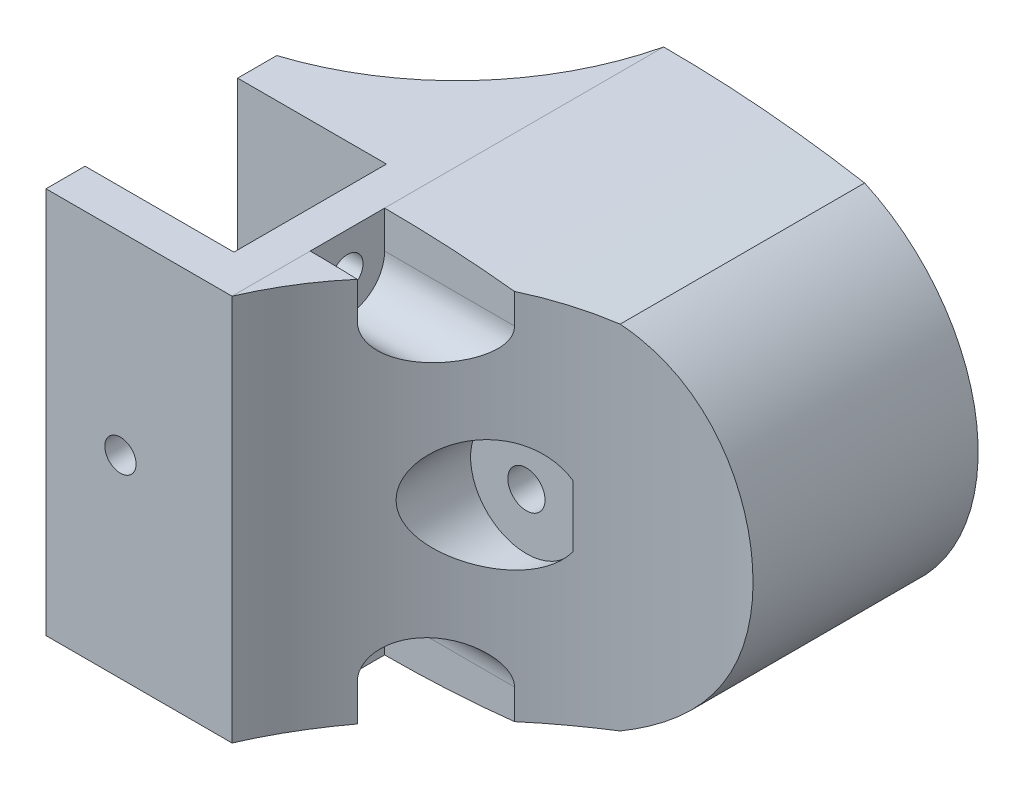
SolidWorks part; units mm, degrees
material "PBT Общее назначение"
ref_plane "Спереди" through (0, 0, 0) normal (0, 0, 1) x (1, 0, 0)
ref_plane "Сверху" through (0, 0, 0) normal (0, 1, 0) x (1, 0, 0)
ref_plane "Справа" through (0, 0, 0) normal (1, 0, 0) x (0, 0, -1)
sketch "Эскиз1" plane through (0, 0, 0) normal (0, 0, 1) x (1, 0, 0)
  line L0 (0, 0) -> (61.556, 0) construction
  line L1 (0, 26) -> (0, -26)
  line L2 (0, 26) -> (52, 26)
  line L3 (0, -26) -> (52, -26)
  line L4 (52, 26) -> (52, -26)
  line L5 (0, 0) -> (52, 0) construction
  dimension "D1" = 52
  dimension "D2" = 52
extrude "Бобышка-Вытянуть1" add sketch "Эскиз1" along normal blind 31
sketch "Эскиз2" plane through (0, 0, 0) normal (-1, 0, 0) x (0, 0, 1)
  line L0 (15.5, 26) -> (15.5, -26) construction
  line L1 (31, 26) -> (0, 26) construction
  line L2 (31, -26) -> (0, -26) construction
  line L3 (5.25, 26) -> (25.75, 26)
  line L4 (5.25, 26) -> (5.25, -26)
  line L5 (25.75, 26) -> (25.75, -26)
  line L6 (5.25, -26) -> (25.75, -26)
  line L7 (15.5, 26) -> (15.5, -26) construction
  dimension "D1" = 20.5
extrude "Вырез-Вытянуть1" cut sketch "Эскиз2" against normal blind 20
sketch "Эскиз3" plane through (52, 0, 0) normal (1, 0, 0) x (0, 0, -1)
  line L0 (-15.5, 26) -> (-15.5, -26) construction
  line L1 (-31, 26) -> (0, 26) construction
  line L2 (-31, -26) -> (0, -26) construction
  line L3 (-31, 0) -> (0, 0) construction
  line L4 (-31, -26) -> (-31, 26) construction
  line L5 (0, -26) -> (0, 26) construction
ref_plane "СимZ" through (0, 0, 15.5) normal (0, 0, 1) x (0, -1, 0)
ref_plane "СимY" through (0, 0, 0) normal (0, -1, 0) x (0, 0, -1)
sketch "Эскиз4" plane through (0, 26, 0) normal (0, 1, 0) x (1, 0, 0)
  line L0 (41.25, 0) -> (41.25, -31) construction
  line L1 (52, 0) -> (0, 0) construction
  line L2 (52, -31) -> (0, -31) construction
  line L3 (20, -25.75) -> (20, -5.25) construction
  line L4 (20, -25.75) -> (20, -5.25) construction
  dimension "D1" = 21.25
ref_plane "Симм Лента" through (41.25, 0, 0) normal (-1, 0, 0) x (0, 0, 1)
sketch "Эскиз5" plane through (0, 0, 31) normal (0, 0, 1) x (1, 0, 0)
  line L0 (41.25, 26) -> (41.25, -26) construction
  line L1 (0, -26) -> (52, -26) construction
  line L2 (52, 26) -> (0, 26) construction
  circle A0 centre (41.25, 0) radius 26
extrude "Бобышка-Вытянуть2" add sketch "Эскиз5" against normal up to surface (31 mm away) up to face at (26, 0, 0)
sketch "Эскиз6" plane through (0, 0, 31) normal (0, 0, 1) x (1, 0, 0)
  line L2 (52, 23.6736) -> (52, 26) construction
  line L3 (52, 26) -> (0, 26) construction
  line L4 (52, 23.6736) -> (52, 26)
  line L5 (52, 26) -> (25, 26)
  arc A0 (52, 23.6736) -> (25, 26) centre (25, -131.8405) ccw
  dimension "D1" = 25
extrude "Вырез-Вытянуть2" cut sketch "Эскиз6" against normal through all
mirror "Зеркальное отражение1" about plane through (0, 0, 0) normal (0, -1, 0) of "Вырез-Вытянуть2"
sketch "Эскиз7" plane through (0, 26, 0) normal (0, 1, 0) x (1, 0, 0)
  line L0 (20, -25.75) -> (20, -5.25) construction
  line L1 (20, -25.75) -> (0, -25.75) construction
  line L2 (20, -5.25) -> (0, -5.25) construction
  line L3 (20, -25.75) -> (20, -5.25)
  line L4 (20, -25.75) -> (0, -25.75)
  line L5 (20, -5.25) -> (0, -5.25)
  line L6 (0, -5.25) -> (0, -25.75)
extrude "Вырез-Вытянуть3" cut sketch "Эскиз7" against normal through all
sketch "Эскиз8" plane through (0, 26, 0) normal (0, 1, 0) x (1, 0, 0)
  line L0 (35.2, 15.75) -> (47.3, 15.75) construction
  line L1 (35.2, 15.75) -> (47.3, 15.75) construction
  line L2 (47.3, 8.35) -> (35.2, 8.35) construction
  line L3 (47.3, 8.35) -> (35.2, 8.35) construction
  line L4 (25, 0) -> (0, 0) construction
  dimension "D1" = 8.35
  dimension "D2" = 15.75
sketch "Эскиз9" plane through (0, 0, 0) normal (0, 0, -1) x (-1, 0, 0)
  line L0 (-25, 26) -> (-25, -26)
  arc A0 (-25, 26) -> (-52, 23.6736) centre (-25, -131.8405) ccw construction
  arc A1 (-52, 23.6736) -> (-52, -23.6736) centre (-41.25, 0) ccw construction
  arc A2 (-52, -23.6736) -> (-25, -26) centre (-25, 131.8405) ccw construction
  arc A3 (-25, 26) -> (-52, 23.6736) centre (-25, -131.8405) ccw
  arc A4 (-52, 23.6736) -> (-52, -23.6736) centre (-41.25, 0) ccw
  arc A5 (-52, -23.6736) -> (-25, -26) centre (-25, 131.8405) ccw
extrude "Бобышка-Вытянуть3" add sketch "Эскиз9" along normal blind 27
sketch "Эскиз10" plane through (41.25, 0, 0) normal (-1, 0, 0) x (0, 0, 1)
  line L0 (0, -26) -> (0, 26) construction
  line L1 (0, -26) -> (0, 26) construction
  line L2 (-6.75, 9) -> (-15.75, 9) construction
  line L3 (-6.75, 9) -> (-6.75, -9) construction
  line L4 (-15.75, 9) -> (-15.75, -9) construction
  line L5 (-6.75, -9) -> (-15.75, -9) construction
  line L6 (-15.75, 0) -> (-6.75, 0) construction
  line L7 (-27, -26) -> (-27, 26) construction
  line L8 (-27, -26) -> (-27, 26) construction
  line L9 (-27, 0) -> (0, 0) construction
  line L10 (-11.25, 9) -> (-11.25, -9) construction
  line L11 (-20.75, 14) -> (-1.75, 14)
  line L12 (-20.75, 14) -> (-20.75, 0)
  line L13 (-20.75, 0) -> (-1.75, 0)
  line L14 (-1.75, 0) -> (-1.75, 14)
  dimension "D1" = 15.75
  dimension "D2" = 9
  dimension "D3" = 18
  dimension "D4" = 5
  dimension "D5" = 5
  dimension "D6" = 5
revolve "Вырез-Повернуть2" cut sketch "Эскиз10" angle 360 about L13
sketch "Эскиз11" plane through (0, 0, 0) normal (0, -1, 0) x (0, 0, -1)
  line L0 (1.75, 27.25) -> (1.75, 55.25) construction
  line L1 (1.75, 27.25) -> (1.75, 55.25)
  line L2 (20.75, 55.25) -> (20.75, 27.25) construction
  line L3 (20.75, 55.25) -> (20.75, 27.25)
  line L4 (20.75, 55.25) -> (1.75, 55.25)
  line L5 (20.75, 27.25) -> (1.75, 27.25)
extrude "Вырез-Вытянуть4" cut sketch "Эскиз11" along normal through all
sketch "Эскиз12" plane through (0, -26, 0) normal (0, -1, 0) x (1, 0, 0)
  line L0 (0, 0) -> (25, 0) construction
  line L1 (25, -27) -> (25, 0) construction
  line L2 (0, 0) -> (25, 0)
  line L3 (25, -27) -> (25, 0)
  arc A0 (25, -27) -> (0, 0) centre (-11.4767, -35.7006) ccw
  dimension "D1" = 75
extrude "Бобышка-Вытянуть4" add sketch "Эскиз12" against normal up to surface (52 mm away) up to face at (11.25, 26, 15.5)
sketch "Эскиз13" plane through (0, 0, 31) normal (0, 0, 1) x (1, 0, 0)
  line L0 (10, -26) -> (10, 26) construction
  line L4 (20, 26) -> (0, 26)
  line L5 (20, -26) -> (20, 26)
  line L6 (0, -26) -> (20, -26)
  line L7 (0, 26) -> (0, -26)
  line L8 (20, 26) -> (0, 26) construction
  line L9 (20, -26) -> (20, 26) construction
  line L10 (0, -26) -> (20, -26) construction
  line L11 (0, 26) -> (0, -26) construction
  circle A0 centre (10, 0) radius 2.1
  dimension "D2" = 4.2
  dimension "D1" = 0
extrude "Вырез-Вытянуть5" cut sketch "Эскиз13" against normal through all
sketch "Эскиз14" plane through (20, 0, 0) normal (-1, 0, 0) x (0, 0, 1)
  line L0 (15.5, -26) -> (15.5, 26) construction
  line L4 (5.25, 26) -> (5.25, -26)
  line L5 (5.25, -26) -> (25.75, -26)
  line L6 (25.75, -26) -> (25.75, 26)
  line L7 (25.75, 26) -> (5.25, 26)
  line L8 (5.25, 26) -> (5.25, -26) construction
  line L9 (5.25, -26) -> (25.75, -26) construction
  line L10 (25.75, -26) -> (25.75, 26) construction
  line L11 (25.75, 26) -> (5.25, 26) construction
  circle A0 centre (15.5, -21) radius 2.1
  circle A1 centre (15.5, 21) radius 2.1
  dimension "D2" = 5
  dimension "D3" = 4.2
  dimension "D4" = 4.2
  dimension "D5" = 5
  dimension "D1" = 0
extrude "Вырез-Вытянуть6" cut sketch "Эскиз14" against normal through all
ref_plane "Плоскость1" through (25, 0, 0) normal (1, 0, 0) x (0, 0, -1)
sketch "Эскиз15" plane through (25, 0, 0) normal (1, 0, 0) x (0, 0, -1)
  circle A0 centre (-15.5, 21) radius 2.1 construction
  circle A1 centre (-15.5, 21) radius 2.1 construction
  circle A2 centre (-15.5, -21) radius 2.1 construction
  circle A3 centre (-15.5, -21) radius 2.1 construction
  circle A4 centre (-15.5, 21) radius 5
  circle A5 centre (-15.5, -21) radius 5
  dimension "D1" = 10
  dimension "D2" = 10
extrude "Вырез-Вытянуть7" cut sketch "Эскиз15" along normal through all
sketch "Эскиз16" plane through (20, 0, 0) normal (-1, 0, 0) x (0, 0, 1)
  line L0 (17.6, 21) -> (13.4, 21) construction
  circle A0 centre (15.5, 21) radius 2.1 construction
ref_plane "Плоскость2" through (0, 21, 0) normal (0, 1, 0) x (0, 0, -1)
sketch "Эскиз17" plane through (0, 21, 0) normal (0, 1, 0) x (0, 0, -1)
  line L0 (-20.5, -25) -> (-10.5, -25) construction
  line L1 (-20.5, -25) -> (-10.5, -25)
  line L2 (-10.5, -25) -> (-10.5, -67.25)
  line L3 (-20.5, -25) -> (-20.5, -67.25)
  line L5 (27, -67.25) -> (27, -52) construction
  line L6 (27, -67.25) -> (27, -52) construction
  line L7 (-10.5, -67.25) -> (-20.5, -67.25)
  line L8 (27, -67.25) -> (-10.5, -67.25) construction
extrude "Вырез-Вытянуть8" cut sketch "Эскиз17" along normal through all
mirror "Зеркальное отражение2" about plane through (0, 0, 0) normal (0, -1, 0) of "Вырез-Вытянуть8"
ref_plane "Плоскость3" through (0, 0, 0) normal (0, 0, -1) x (-1, 0, 0)
sketch "Эскиз18" plane through (0, 0, 0) normal (0, 0, -1) x (-1, 0, 0)
  circle A0 centre (-10, 0) radius 2.1 construction
  circle A1 centre (-10, 0) radius 2.1 construction
  circle A2 centre (-10, 0) radius 5
  dimension "D1" = 10
extrude "Вырез-Вытянуть9" cut sketch "Эскиз18" along normal through all
sketch "Эскиз19" plane through (0, 0, 31) normal (0, 0, 1) x (1, 0, 0)
  arc A0 (52, -23.6736) -> (52, 23.6736) centre (41.25, 0) ccw construction
  arc A1 (52, -23.6736) -> (52, 23.6736) centre (41.25, 0) ccw construction
  circle A2 centre (41.25, 0) radius 26 construction
  circle A3 centre (41.25, 0) radius 2.5
  dimension "D1" = 5
extrude "Вырез-Вытянуть10" cut sketch "Эскиз19" against normal through all
sketch "Sketch1" plane through (0, 26, 0) normal (0, 1, 0) x (1, 0, 0)
  line L14 (67.25, 27) -> (52, 27) construction
  line L15 (67.25, 27) -> (52, 27) construction
  line L16 (52, -31) -> (67.25, -31) construction
  line L17 (25, -31) -> (67.25, -31)
  line L18 (67.25, -31) -> (67.25, -3.25)
  line L19 (52, 1.75) -> (27.25, 1.75) construction
  line L20 (52, 1.75) -> (27.25, 1.75) construction
  line L21 (28.1092, -3.25) -> (67.25, -3.25) construction
  line L23 (67.25, -3.25) -> (67.25, 27) construction
  arc A0 (67.25, -3.25) -> (25, -31) centre (67.25, -49.2883) ccw
  point P10 (67.25, -3.25)
  dimension "D2" = 5
extrude "Cut-Extrude1" cut sketch "Sketch1" against normal through all
sketch "Sketch2" plane through (0, 0, 0) normal (0, -1, 0) x (0, 0, -1)
  line L0 (-9.6995, 43.75) -> (-9.6995, -35.6568) construction
  line L1 (20.75, 43.75) -> (20.75, 38.75) construction
  line L2 (20.75, 43.75) -> (20.75, 38.75) construction
  line L3 (20.75, 41.25) -> (-31.3718, 41.25) construction
  arc A0 (-13.132, 38.75) -> (-9.6995, 43.75) centre (-49.2883, 67.25) ccw construction
  arc A1 (-13.132, 38.75) -> (-9.6995, 43.75) centre (-49.2883, 67.25) ccw construction
ref_plane "Plane1" through (0, 0, 9.6995) normal (0, 0, 1) x (1, 0, 0)
sketch "Sketch3" plane through (0, 0, 9.6995) normal (0, 0, 1) x (1, 0, 0)
  circle A0 centre (41.25, 0) radius 2.5 construction
  circle A1 centre (41.25, 0) radius 2.5 construction
  circle A2 centre (41.25, 0) radius 7.5
  dimension "D1" = 15
extrude "Cut-Extrude2" cut sketch "Sketch3" along normal through all and the other way blind 2
sketch "Эскиз20" plane through (0, 0, 0) normal (0, 0, -1) x (-1, 0, 0)
  line L0 (-10, 5) -> (0, 5)
  line L1 (0, 26) -> (0, -26) construction
  line L2 (0, 5) -> (0, -5)
  line L3 (-15, 0) -> (-15, -5)
  line L4 (-15, -5) -> (0, -5)
  circle A0 centre (-10, 0) radius 5 construction
  arc A1 (-10, 5) -> (-15, 0) centre (-10, 0) ccw
extrude "Вырез-Вытянуть11" cut sketch "Эскиз20" along normal through all
sketch "Эскиз21" plane through (0, -5, 0) normal (0, 1, 0) x (1, 0, 0)
  line L0 (15, 9.1444) -> (0, 9.1444)
  line L1 (0, 9.1444) -> (0, 0)
  line L2 (0, 0) -> (15, 0)
  line L3 (15, 0) -> (15, 9.1444)
  line L4 (0, 0) -> (15, 0)
  line L5 (15, 0) -> (15, 9.1444)
  arc A1 (0, 0) -> (15, 9.1444) centre (-11.4767, 35.7006) ccw
  dimension "D1" = 0
extrude "Бобышка-Вытянуть5" add sketch "Эскиз21" against normal up to surface (21 mm away) up to face at (14.3539, -26, 13.1277)
sketch "Эскиз22" plane through (0, -26, 0) normal (0, -1, 0) x (1, 0, 0)
  line L0 (0, 5.25) -> (0, -9.1444) construction
  line L1 (10, 1.9254) -> (7.25, 0.3377)
  line L2 (7.25, 0.3377) -> (7.25, -2.8377)
  line L3 (7.25, -2.8377) -> (10, -4.4254)
  line L4 (10, -4.4254) -> (12.75, -2.8377)
  line L5 (12.75, -2.8377) -> (12.75, 0.3377)
  line L6 (12.75, 0.3377) -> (10, 1.9254)
  line L7 (20, 5.25) -> (0, 5.25) construction
  line L8 (10, -1.25) -> (10, -4.4254) construction
  circle A0 centre (10, -1.25) radius 2.75 construction
  dimension "D1" = 10
  dimension "D2" = 6.5
  dimension "D3" = 5.5
extrude "Вырез-Вытянуть12" cut sketch "Эскиз22" against normal blind 15
fillet "Скругление1" radius 3 1 edges at (0, -15.5, -9.1444)
